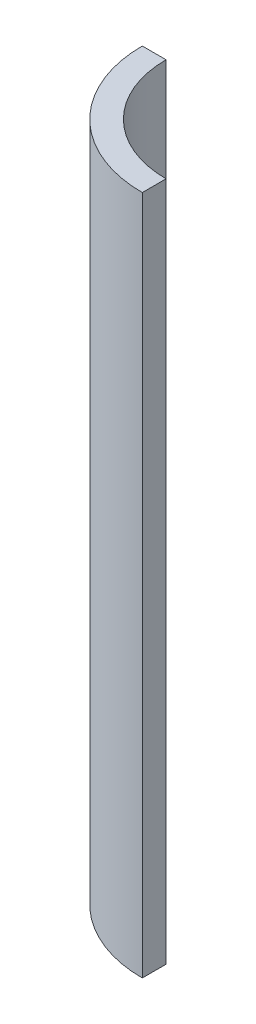
SolidWorks part; units mm, degrees
ref_plane "Front Plane" through (0, 0, 0) normal (0, 0, 1) x (1, 0, 0)
ref_plane "Top Plane" through (0, 0, 0) normal (0, 1, 0) x (1, 0, 0)
ref_plane "Right Plane" through (0, 0, 0) normal (1, 0, 0) x (0, 0, -1)
sketch "Sketch1" plane through (0, 0, 0) normal (0, 1, 0) x (1, 0, 0)
  line L0 (0, -82.55) -> (0, -101.6)
  line L1 (-82.55, 0) -> (-101.6, 0)
  arc A0 (-82.55, 0) -> (0, -82.55) centre (0, 0) ccw
  arc A1 (-101.6, 0) -> (0, -101.6) centre (0, 0) ccw
  dimension "D1" = 203.2
  dimension "D2" = 165.1
extrude "Boss-Extrude1" add sketch "Sketch1" along normal blind 544.576
